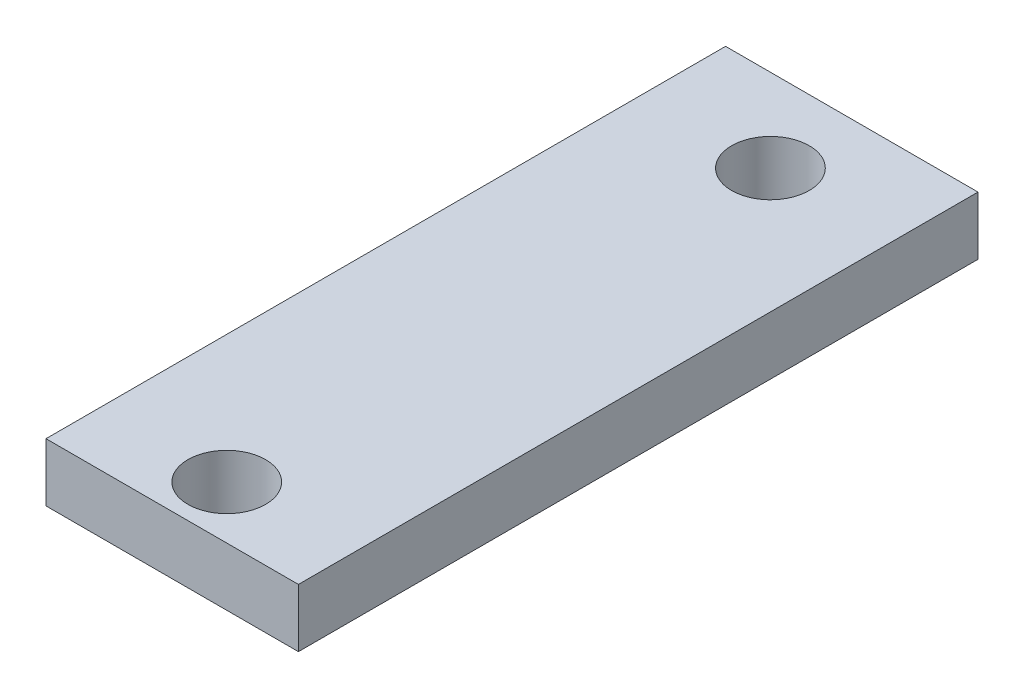
SolidWorks part; units mm, degrees
ref_plane "Front Plane" through (0, 0, 0) normal (0, 0, 1) x (1, 0, 0)
ref_plane "Top Plane" through (0, 0, 0) normal (0, 1, 0) x (1, 0, 0)
ref_plane "Right Plane" through (0, 0, 0) normal (1, 0, 0) x (0, 0, -1)
sketch "Sketch2" plane through (0, 0, 0) normal (0, 1, 0) x (1, 0, 0)
  line L40 (68.5884, 19.1276) -> (81.5884, 19.1276)
  line L61 (68.5884, 54.1276) -> (68.5884, 19.1276)
  line L63 (81.5884, 54.1276) -> (68.5884, 54.1276)
  line L65 (81.5884, 19.1276) -> (81.5884, 54.1276)
  circle A62 centre (75.1751, 49.8502) radius 2
  circle A63 centre (75.1751, 21.8502) radius 2
extrude "Boss-Extrude1" add sketch "Sketch2" along normal blind 3
